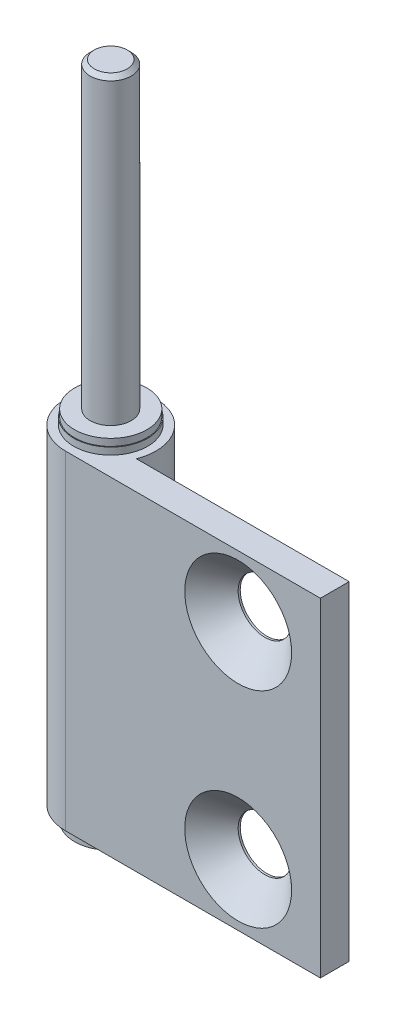
SolidWorks part; units mm, degrees
ref_plane "Piano frontale" through (0, 0, 0) normal (0, 0, 1) x (1, 0, 0)
ref_plane "Piano superiore" through (0, 0, 0) normal (0, 1, 0) x (1, 0, 0)
ref_plane "Piano destro" through (0, 0, 0) normal (1, 0, 0) x (0, 0, -1)
ref_plane "Plane1" through (0, -41.7, 0) normal (0, -1, 0) x (1, 0, 0)
sketch "Sketch1" plane through (0, -41.7, 0) normal (0, -1, 0) x (1, 0, 0)
  line L0 (31, 5.5) -> (0, 5.5)
  line L1 (5.1235, 2) -> (31, 2)
  line L2 (31, 2) -> (31, 5.5)
  arc A0 (0, 5.5) -> (5.1235, 2) centre (0, 0) ccw
extrude "Extrude1" add sketch "Sketch1" against normal blind 40
sketch "Sketch2" plane through (0, 0, 0) normal (0, 0, 1) x (1, 0, 0)
  line L0 (2.5, 36.8) -> (0, 36.8)
  line L1 (0, 36.8) -> (0, -1.7)
  line L2 (0, -1.7) -> (4.5, -1.7)
  line L3 (4.5, -1.7) -> (4.5, -0.85)
  line L4 (4.5, -0.85) -> (4.4, -0.85)
  line L5 (4.4, -0.85) -> (4.4, 0)
  line L6 (4.4, 0) -> (2.5, 0)
  line L7 (2.5, 0) -> (2.5, 36.8)
  line L8 (0, 36.8) -> (0, -1.7) construction
revolve "Revolve1" add sketch "Sketch2" angle 360 about L8
sketch "Sketch3" plane through (0, 0, 0) normal (0, 0, 1) x (1, 0, 0)
  line L0 (4.5, -41.7) -> (0, -41.7)
  line L1 (0, -41.7) -> (0, -44.9)
  line L2 (0, -44.9) -> (2.5, -44.9)
  line L3 (2.5, -44.9) -> (2.5, -43.4)
  line L4 (2.5, -43.4) -> (4.4, -43.4)
  line L5 (4.4, -43.4) -> (4.4, -42.55)
  line L6 (4.4, -42.55) -> (4.5, -42.55)
  line L7 (4.5, -42.55) -> (4.5, -41.7)
  line L8 (0, -41.7) -> (0, -44.9) construction
revolve "Revolve2" add sketch "Sketch3" angle 360 about L8
hole_wizard "HoleWzd1" positions "Sketch5" profile "Sketch4" countersink size "M6" standard "Ansi Metric"
sketch "Sketch5" plane through (0, 0, 5.5) normal (0, 0, 1) x (1, 0, 0)
  point P0 (21, -34.2)
  point P1 (21, -9.2)
sketch "Sketch4" plane through (21, -34.2, 5.5) normal (1, 0, 0) x (0, -1, 0)
  line L0 (0, 0) -> (0, 11)
  line L1 (0, 11) -> (3.25, 11)
  line L2 (3.25, 11) -> (3.25, 3.25)
  line L3 (3.25, 3.25) -> (6.5, 0)
  line L5 (6.5, 0) -> (0, 0)
  line L6 (-3.25, 3.25) -> (-6.5, 0) construction
  line L11 (0, -6.35) -> (0, 107.95) construction
  dimension "Thru Hole Dia." = 6.5
  dimension "Thru Hole Depth" = 11
  dimension "Near C'Sink Dia." = 13
  dimension "Near C'Sink Angle" = 90
chamfer "Chamfer1" distance 0.5 angle 45 2 edges at (0, 36.8, -2.5) (0, -44.9, -2.5)
